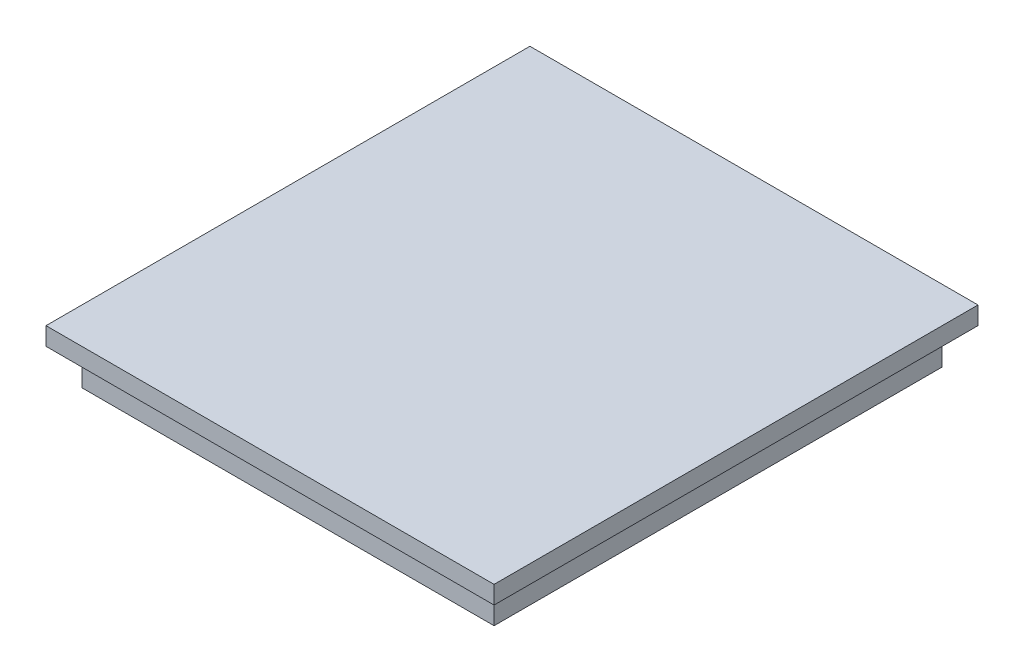
SolidWorks part; units mm, degrees
material "ABS"
ref_plane "Front" through (0, 0, 0) normal (0, 0, 1) x (1, 0, 0)
ref_plane "Top" through (0, 0, 0) normal (0, 1, 0) x (1, 0, 0)
ref_plane "Right" through (0, 0, 0) normal (1, 0, 0) x (0, 0, -1)
sketch "Sketch1" plane through (0, 0, 0) normal (0, 1, 0) x (1, 0, 0)
  line L1 (-57.5, 62.5) -> (57.5, 62.5)
  line L2 (-57.5, 62.5) -> (-57.5, -62.5)
  line L3 (-57.5, -62.5) -> (57.5, -62.5)
  line L4 (57.5, 62.5) -> (57.5, -62.5)
  line L5 (-57.5, 62.5) -> (57.5, -62.5) construction
  line L6 (-57.5, -62.5) -> (57.5, 62.5) construction
  point P0 (0, 0)
  dimension "D1" = 115
  dimension "D2" = 125
extrude "Boss-Extrude1" add sketch "Sketch1" along normal blind 10
sketch "Sketch2" plane through (0, 10, 0) normal (0, 1, 0) x (1, 0, 0)
  line L1 (-62.5, 67.5) -> (62.5, 67.5)
  line L2 (-62.5, 67.5) -> (-62.5, -67.5)
  line L3 (-62.5, -67.5) -> (62.5, -67.5)
  line L4 (62.5, 67.5) -> (62.5, -67.5)
  line L5 (-62.5, 67.5) -> (62.5, -67.5) construction
  line L6 (-62.5, -67.5) -> (62.5, 67.5) construction
  point P0 (0, 0)
  dimension "D1" = 135
  dimension "D2" = 125
extrude "Boss-Extrude2" add sketch "Sketch2" along normal blind 5
